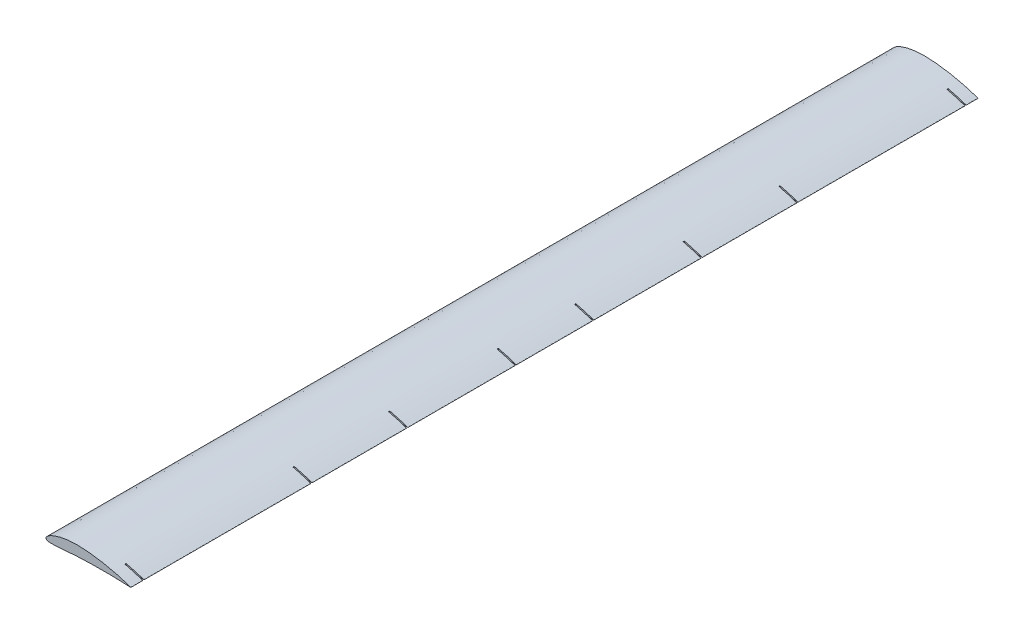
SolidWorks part; units mm, degrees
ref_plane "Front Plane" through (0, 0, 0) normal (0, 0, 1) x (1, 0, 0)
ref_plane "Top Plane" through (0, 0, 0) normal (0, 1, 0) x (1, 0, 0)
ref_plane "Right Plane" through (0, 0, 0) normal (1, 0, 0) x (0, 0, -1)
curve "Curve1"
  spline degree 3 poles (355.3888, 0.4406, 0) (355.0726, 0.5495, 0) (353.8127, 0.9836, 0) (350.9924, 1.9569, 0) (346.3157, 3.5272, 0) (339.832, 5.6651, 0) (331.5966, 8.2829, 0) (321.6863, 11.2988, 0) (310.1986, 14.6185, 0) (297.2438, 18.1374, 0) (282.9525, 21.7494, 0) (267.4682, 25.3403, 0) (250.9566, 28.8199, 0) (233.5901, 32.0756, 0) (215.5559, 35.0116, 0) (197.0522, 37.5517, 0) (178.2867, 39.6142, 0) (159.4608, 41.1338, 0) (140.6596, 42.1318, 0) (122.084, 42.2492, 0) (103.9936, 41.3416, 0) (86.7639, 39.4997, 0) (70.6227, 36.8321, 0) (55.7825, 33.4553, 0) (42.4293, 29.5342, 0) (30.7191, 25.2445, 0) (20.778, 20.7597, 0) (12.7, 16.2527, 0) (6.5212, 11.8828, 0) (2.2745, 7.7449, 0) (-0.17, 3.8261, 0) (-0.3916, -0.118, 0) (1.9464, -3.2779, 0) (6.0452, -5.2566, 0) (11.6804, -6.5557, 0) (18.9405, -7.2366, 0) (27.7531, -7.3729, 0) (38.034, -7.0219, 0) (49.6673, -6.2701, 0) (62.5336, -5.2066, 0) (76.5078, -3.9527, 0) (91.4639, -2.6159, 0) (107.2725, -1.3118, 0) (123.8022, -0.1619, 0) (141.0476, 0.7046, 0) (158.8551, 1.3167, 0) (177.0383, 1.9477, 0) (195.2807, 2.4518, 0) (213.3789, 2.8168, 0) (231.1399, 3.0215, 0) (248.3679, 3.058, 0) (264.8711, 2.937, 0) (280.4633, 2.686, 0) (294.9648, 2.3126, 0) (308.2055, 1.8819, 0) (320.0343, 1.401, 0) (330.2859, 0.9429, 0) (338.9054, 0.457, 0) (345.5919, 0.2217, 0) (350.7414, -0.376, 0) (353.2933, -0.0051, 0) (355.2573, -0.7277, 0) (355.2899, -0.1722, 0) (355.3, 0, 0) knots 0 0 0 0 0.001372 0.005465 0.012235 0.021602 0.033461 0.047671 0.064081 0.082496 0.102719 0.124527 0.147676 0.171913 0.196978 0.222597 0.248497 0.274385 0.300041 0.32569 0.350525 0.37428 0.396711 0.417577 0.436654 0.453744 0.46868 0.481329 0.491631 0.499616 0.505546 0.510185 0.514824 0.520702 0.528516 0.538466 0.550543 0.564643 0.580638 0.598345 0.617584 0.638174 0.659922 0.682632 0.706121 0.730727 0.7557 0.780732 0.805564 0.829932 0.85357 0.876213 0.89761 0.917519 0.935698 0.951943 0.966047 0.97784 0.987174 0.993932 0.998018 0.999386 1 1 1 1
sketch "Sketch1" plane through (0, 0, 0) normal (0, 0, 1) x (1, 0, 0)
  line L0 (355.3888, 0.4406) -> (355.3, 0)
  spline S0 degree 3 poles (-199.9504, -2931.1866) (613.548, -80.7899) (481.8677, -43.2097) (350.9924, 1.9569) (346.3157, 3.5272) (339.832, 5.6651) (331.5966, 8.2829) (321.6863, 11.2988) (310.1986, 14.6185) (297.2438, 18.1374) (282.9525, 21.7494) (267.4682, 25.3403) (250.9566, 28.8199) (233.5901, 32.0756) (215.5559, 35.0116) (197.0522, 37.5517) (178.2867, 39.6142) (159.4608, 41.1338) (140.6596, 42.1318) (122.084, 42.2492) (103.9936, 41.3416) (86.7639, 39.4997) (70.6227, 36.8321) (55.7825, 33.4553) (42.4293, 29.5342) (30.7191, 25.2445) (20.778, 20.7597) (12.7, 16.2527) (6.5212, 11.8828) (2.2745, 7.7449) (-0.17, 3.8261) (-0.3916, -0.118) (1.9464, -3.2779) (6.0452, -5.2566) (11.6804, -6.5557) (18.9405, -7.2366) (27.7531, -7.3729) (38.034, -7.0219) (49.6673, -6.2701) (62.5336, -5.2066) (76.5078, -3.9527) (91.4639, -2.6159) (107.2725, -1.3118) (123.8022, -0.1619) (141.0476, 0.7046) (158.8551, 1.3167) (177.0383, 1.9477) (195.2807, 2.4518) (213.3789, 2.8168) (231.1399, 3.0215) (248.3679, 3.058) (264.8711, 2.937) (280.4633, 2.686) (294.9648, 2.3126) (308.2055, 1.8819) (320.0343, 1.401) (330.2859, 0.9429) (338.9054, 0.457) (345.5919, 0.2217) (350.7414, -0.376) (353.2933, -0.0051) (361.5237, -3.0331) (297.8087, 86.2429) (2187.9364, -2365.1034) knots -0.555523 -0.555523 -0.555523 -0.555523 0.001372 0.005465 0.012235 0.021602 0.033461 0.047671 0.064081 0.082496 0.102719 0.124527 0.147676 0.171913 0.196978 0.222597 0.248497 0.274385 0.300041 0.32569 0.350525 0.37428 0.396711 0.417577 0.436654 0.453744 0.46868 0.481329 0.491631 0.499616 0.505546 0.510185 0.514824 0.520702 0.528516 0.538466 0.550543 0.564643 0.580638 0.598345 0.617584 0.638174 0.659922 0.682632 0.706121 0.730727 0.7557 0.780732 0.805564 0.829932 0.85357 0.876213 0.89761 0.917519 0.935698 0.951943 0.966047 0.97784 0.987174 0.993932 0.998018 0.999386 1.019362 1.019362 1.019362 1.019362 only from (355.3888, 0.4406) to (355.3, 0) construction
  spline S1 degree 3 poles (355.3888, 0.4406) (355.0726, 0.5495) (353.8127, 0.9836) (350.9924, 1.9569) (346.3157, 3.5272) (339.832, 5.6651) (331.5966, 8.2829) (321.6863, 11.2988) (310.1986, 14.6185) (297.2438, 18.1374) (282.9525, 21.7494) (267.4682, 25.3403) (250.9566, 28.8199) (233.5901, 32.0756) (215.5559, 35.0116) (197.0522, 37.5517) (178.2867, 39.6142) (159.4608, 41.1338) (140.6596, 42.1318) (122.084, 42.2492) (103.9936, 41.3416) (86.7639, 39.4997) (70.6227, 36.8321) (55.7825, 33.4553) (42.4293, 29.5342) (30.7191, 25.2445) (20.778, 20.7597) (12.7, 16.2527) (6.5212, 11.8828) (2.2745, 7.7449) (-0.17, 3.8261) (-0.3916, -0.118) (1.9464, -3.2779) (6.0452, -5.2566) (11.6804, -6.5557) (18.9405, -7.2366) (27.7531, -7.3729) (38.034, -7.0219) (49.6673, -6.2701) (62.5336, -5.2066) (76.5078, -3.9527) (91.4639, -2.6159) (107.2725, -1.3118) (123.8022, -0.1619) (141.0476, 0.7046) (158.8551, 1.3167) (177.0383, 1.9477) (195.2807, 2.4518) (213.3789, 2.8168) (231.1399, 3.0215) (248.3679, 3.058) (264.8711, 2.937) (280.4633, 2.686) (294.9648, 2.3126) (308.2055, 1.8819) (320.0343, 1.401) (330.2859, 0.9429) (338.9054, 0.457) (345.5919, 0.2217) (350.7414, -0.376) (353.2933, -0.0051) (355.2573, -0.7277) (355.2899, -0.1722) (355.3, 0) knots 0 0 0 0 0.001372 0.005465 0.012235 0.021602 0.033461 0.047671 0.064081 0.082496 0.102719 0.124527 0.147676 0.171913 0.196978 0.222597 0.248497 0.274385 0.300041 0.32569 0.350525 0.37428 0.396711 0.417577 0.436654 0.453744 0.46868 0.481329 0.491631 0.499616 0.505546 0.510185 0.514824 0.520702 0.528516 0.538466 0.550543 0.564643 0.580638 0.598345 0.617584 0.638174 0.659922 0.682632 0.706121 0.730727 0.7557 0.780732 0.805564 0.829932 0.85357 0.876213 0.89761 0.917519 0.935698 0.951943 0.966047 0.97784 0.987174 0.993932 0.998018 0.999386 1 1 1 1
extrude "Boss-Extrude1" add sketch "Sketch1" along normal blind 3553
sketch "Sketch2" plane through (0, 0, 0) normal (0, 0, -1) x (-1, 0, 0)
  line L0 (0, 0) -> (-355.3444, 0.2203) construction
  line L1 (-355.3, 0) -> (-355.3888, 0.4406) construction
sketch "Sketch3" plane through (0, 0, 3553) normal (0, 0, 1) x (1, 0, 0)
  line L0 (0, 0) -> (355.3, 0) construction
sketch "Sketch4" plane through (0, 0, 0) normal (0, 1, 0) x (1, 0, 0)
  line L0 (355.3888, -3553) -> (355.3888, 0) construction
  line L1 (430.3888, -50) -> (280.3888, -50)
  line L2 (430.3888, -50) -> (430.3888, -55)
  line L3 (430.3888, -55) -> (280.3888, -55)
  line L4 (280.3888, -50) -> (280.3888, -55)
  line L5 (430.3888, -50) -> (280.3888, -55) construction
  line L6 (430.3888, -55) -> (280.3888, -50) construction
  line L7 (0, 0) -> (355.3444, 0) construction
  line L8 (280.3888, -755) -> (430.3888, -755)
  line L9 (280.3888, -755) -> (280.3888, -760)
  line L10 (280.3888, -760) -> (430.3888, -760)
  line L11 (430.3888, -755) -> (430.3888, -760)
  line L12 (280.3888, -755) -> (430.3888, -760) construction
  line L13 (280.3888, -760) -> (430.3888, -755) construction
  line L14 (430.3888, -1161.5) -> (280.3888, -1161.5)
  line L15 (430.3888, -1161.5) -> (430.3888, -1156.5)
  line L16 (430.3888, -1156.5) -> (280.3888, -1156.5)
  line L17 (280.3888, -1161.5) -> (280.3888, -1156.5)
  line L18 (430.3888, -1161.5) -> (280.3888, -1156.5) construction
  line L19 (430.3888, -1156.5) -> (280.3888, -1161.5) construction
  line L20 (430.3888, -1616.5) -> (280.3888, -1616.5)
  line L21 (430.3888, -1616.5) -> (430.3888, -1611.5)
  line L22 (430.3888, -1611.5) -> (280.3888, -1611.5)
  line L23 (280.3888, -1616.5) -> (280.3888, -1611.5)
  line L24 (430.3888, -1616.5) -> (280.3888, -1611.5) construction
  line L25 (430.3888, -1611.5) -> (280.3888, -1616.5) construction
  line L26 (280.3888, -1936.5) -> (430.3888, -1936.5)
  line L27 (280.3888, -1936.5) -> (280.3888, -1941.5)
  line L28 (280.3888, -1941.5) -> (430.3888, -1941.5)
  line L29 (430.3888, -1936.5) -> (430.3888, -1941.5)
  line L30 (280.3888, -1936.5) -> (430.3888, -1941.5) construction
  line L31 (280.3888, -1941.5) -> (430.3888, -1936.5) construction
  line L32 (280.3888, -2391.5) -> (430.3888, -2391.5)
  line L33 (280.3888, -2391.5) -> (280.3888, -2396.5)
  line L34 (280.3888, -2396.5) -> (430.3888, -2396.5)
  line L35 (430.3888, -2391.5) -> (430.3888, -2396.5)
  line L36 (280.3888, -2391.5) -> (430.3888, -2396.5) construction
  line L37 (280.3888, -2396.5) -> (430.3888, -2391.5) construction
  line L38 (280.3888, -2798) -> (430.3888, -2798)
  line L39 (280.3888, -2798) -> (280.3888, -2793)
  line L40 (280.3888, -2793) -> (430.3888, -2793)
  line L41 (430.3888, -2798) -> (430.3888, -2793)
  line L42 (280.3888, -2798) -> (430.3888, -2793) construction
  line L43 (280.3888, -2793) -> (430.3888, -2798) construction
  line L44 (280.3888, -3498) -> (430.3888, -3498)
  line L45 (280.3888, -3498) -> (280.3888, -3503)
  line L46 (280.3888, -3503) -> (430.3888, -3503)
  line L47 (430.3888, -3498) -> (430.3888, -3503)
  line L48 (280.3888, -3498) -> (430.3888, -3503) construction
  line L49 (280.3888, -3503) -> (430.3888, -3498) construction
  line L50 (0, -3553) -> (355.3, -3553) construction
  point P0 (355.3888, -52.5)
  point P7 (355.3888, -757.5)
  point P12 (355.3888, -1159)
  point P17 (355.3888, -1614)
  point P22 (355.3888, -1939)
  point P27 (355.3888, -2394)
  point P32 (355.3888, -2795.5)
  point P37 (355.3888, -3500.5)
  point P46 (355.3888, -1776.5)
  dimension "D1" = 150
  dimension "D2" = 5
  dimension "D3" = 5
  dimension "D4" = 150
  dimension "D5" = 5
  dimension "D6" = 150
  dimension "D7" = 5
  dimension "D8" = 150
  dimension "D9" = 5
  dimension "D10" = 150
  dimension "D11" = 5
  dimension "D12" = 150
  dimension "D13" = 5
  dimension "D14" = 150
  dimension "D15" = 5
  dimension "D16" = 150
  dimension "D17" = 50
  dimension "D18" = 50
  dimension "D19" = 700
  dimension "D20" = 700
  dimension "D21" = 160
  dimension "D22" = 160
  dimension "D23" = 450
  dimension "D24" = 450
extrude "Cut-Extrude1" cut sketch "Sketch4" against normal blind 611 and the other way blind 130
